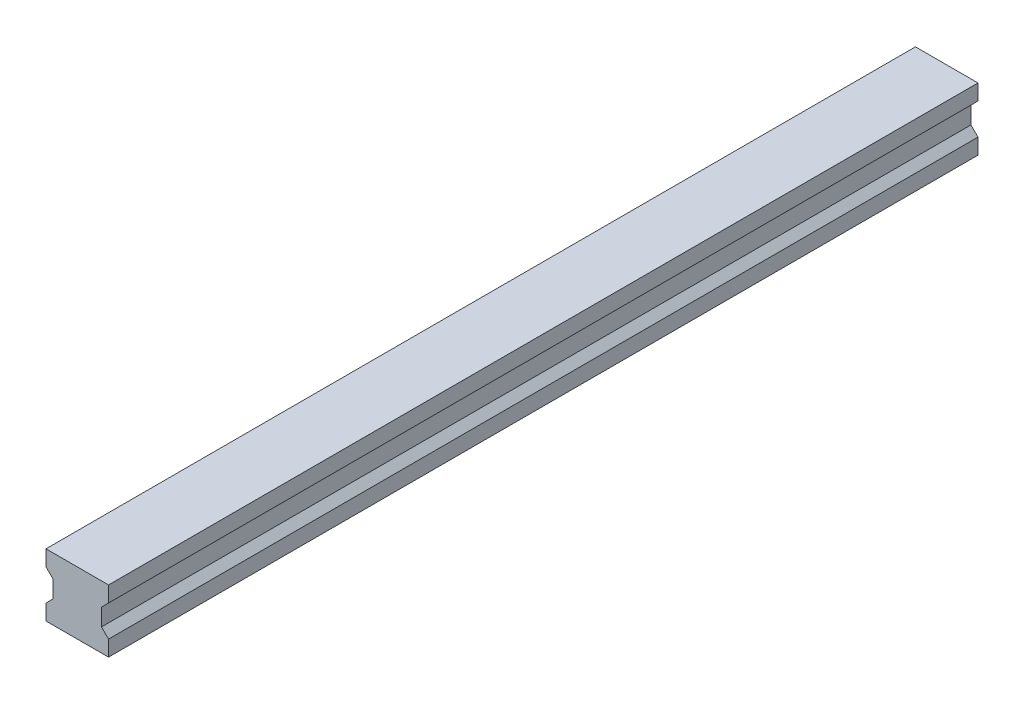
SolidWorks part; units mm, degrees
ref_plane "Front Plane" through (0, 0, 0) normal (0, 0, 1) x (1, 0, 0)
ref_plane "Top Plane" through (0, 0, 0) normal (0, 1, 0) x (1, 0, 0)
ref_plane "Right Plane" through (0, 0, 0) normal (1, 0, 0) x (0, 0, -1)
sketch "Sketch1" plane through (0, 0, 0) normal (0, 0, 1) x (1, 0, 0)
  line L0 (7.75, -2.75) -> (7.75, 2.75)
  line L1 (7.75, 2.75) -> (10, 5)
  line L2 (10, 5) -> (10, 10)
  line L3 (10, 10) -> (-10, 10)
  line L4 (-10, 10) -> (-10, 5)
  line L5 (-10, 5) -> (-7.75, 2.75)
  line L6 (-7.75, 2.75) -> (-7.75, -2.75)
  line L7 (-7.75, -2.75) -> (-10, -5)
  line L8 (-10, -5) -> (-10, -10)
  line L9 (-10, -10) -> (10, -10)
  line L10 (10, -10) -> (10, -5)
  line L11 (10, -5) -> (7.75, -2.75)
extrude "Boss-Extrude1" add sketch "Sketch1" along normal blind 278
